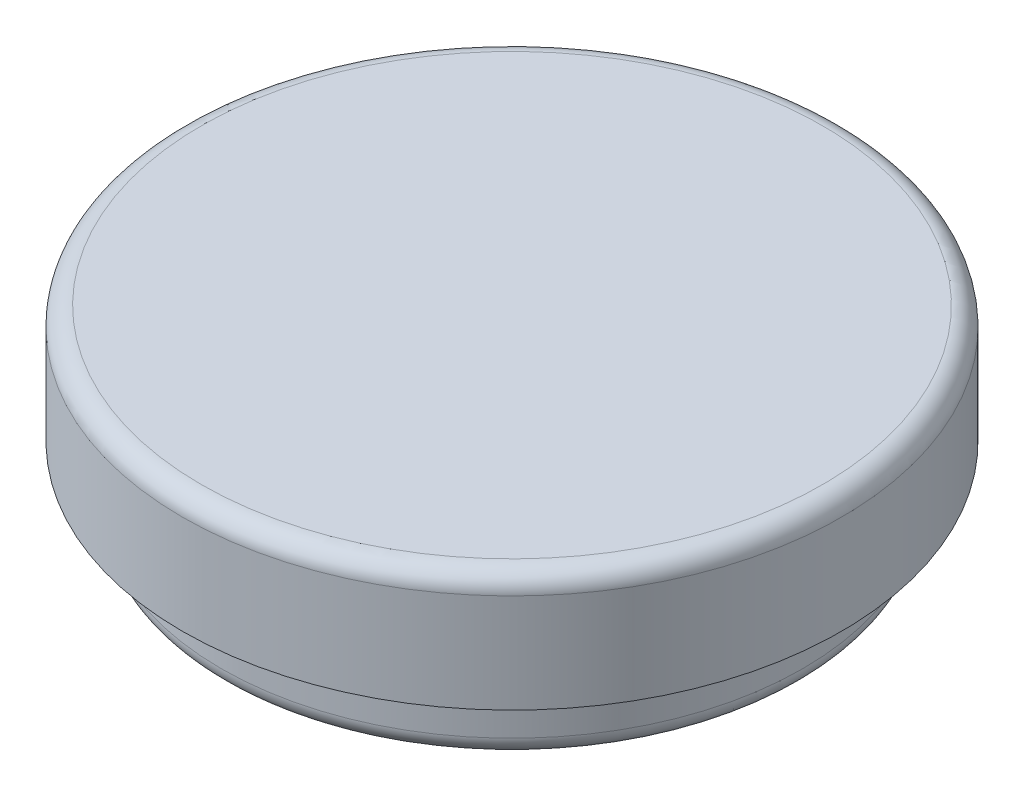
SolidWorks part; units mm, degrees
ref_plane "Спереди" through (0, 0, 0) normal (0, 0, 1) x (1, 0, 0)
ref_plane "Сверху" through (0, 0, 0) normal (0, 1, 0) x (1, 0, 0)
ref_plane "Справа" through (0, 0, 0) normal (1, 0, 0) x (0, 0, -1)
other "Configuration Table"
sketch "Эскиз1" plane through (0, 0, 0) normal (0, 1, 0) x (1, 0, 0)
  circle A0 centre (0, 0) radius 14
  dimension "D1" = 28
extrude "Бобышка-Вытянуть1" add sketch "Эскиз1" along normal blind 5
sketch "Эскиз2" plane through (0, 0, 0) normal (0, -1, 0) x (1, 0, 0)
  circle A0 centre (0, 0) radius 12.35
  dimension "D1" = 24.7
extrude "Бобышка-Вытянуть2" add sketch "Эскиз2" along normal blind 3
sketch "Эскиз3" plane through (0, -3, 0) normal (0, -1, 0) x (1, 0, 0)
  circle A0 centre (0, 0) radius 11
  dimension "D1" = 22
extrude "Вырез-Вытянуть1" cut sketch "Эскиз3" against normal blind 5
fillet "Скругление2" radius 0.8 1 edges at (0, -3, -12.35)
fillet "Скругление3" radius 0.8 1 edges at (0, 5, 14)
